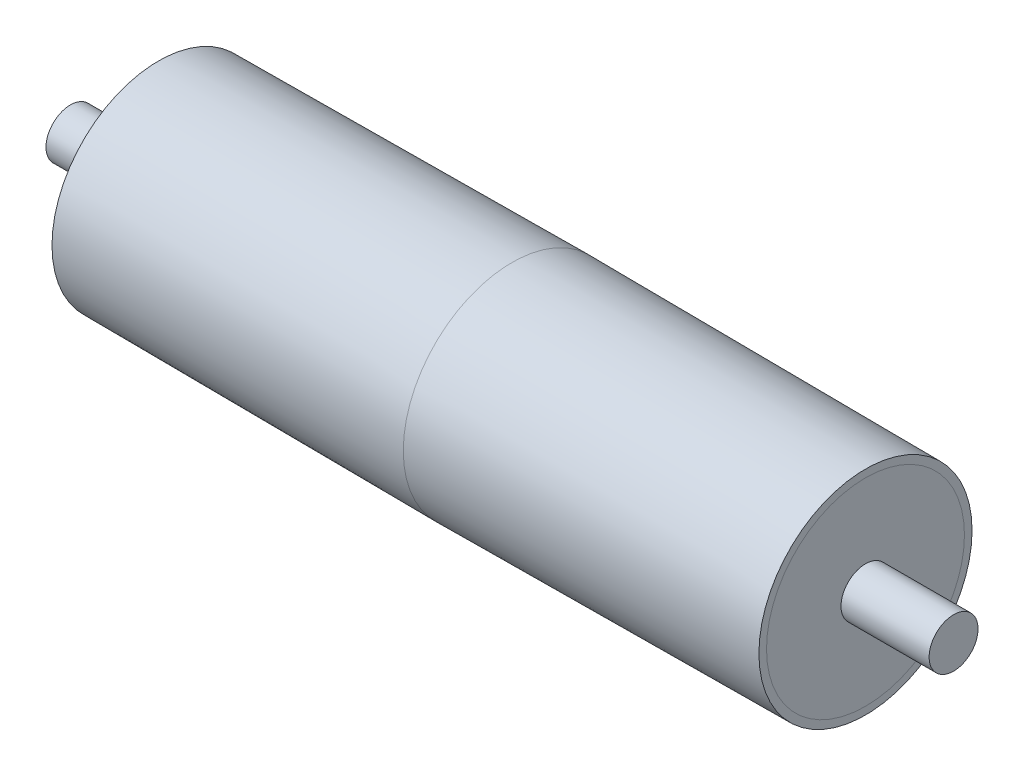
SolidWorks part; units mm, degrees
ref_plane "Front Plane" through (0, 0, 0) normal (0, 0, 1) x (1, 0, 0)
ref_plane "Top Plane" through (0, 0, 0) normal (0, 1, 0) x (1, 0, 0)
ref_plane "Right Plane" through (0, 0, 0) normal (1, 0, 0) x (0, 0, -1)
sketch "Sketch1" plane through (0, 0, 0) normal (0, 0, 1) x (1, 0, 0)
  line L0 (-325, 98) -> (325, 98) construction
  line L1 (-325, 98) -> (0, 100)
  line L2 (0, 0) -> (0, 98) construction
  line L3 (325, 98) -> (0, 100)
  line L4 (0, 0) -> (-22.4876, 0) construction
  line L5 (-325, 98) -> (-325, 0)
  line L6 (-325, 0) -> (325, 0)
  line L7 (325, 0) -> (325, 98)
  point P2 (0, 98)
  dimension "D1" = 2
  dimension "D2" = 650
  dimension "D3" = 100
revolve "Revolve1" add sketch "Sketch1" angle 360 about L6
shell "Shell1" thickness 7
sketch "Sketch2" plane through (325, 0, 0) normal (1, 0, 0) x (0, 0, -1)
  circle A0 centre (0, 0) radius 90.9999
  circle A1 centre (0, 0) radius 90.9999 construction
extrude "Boss-Extrude1" add sketch "Sketch2" against normal blind 10 separate body
mirror "Mirror2" about plane through (0, 0, 0) normal (1, 0, 0) of bodies 102
sketch "Sketch3" plane through (325, 0, 0) normal (1, 0, 0) x (0, 0, -1)
  circle A0 centre (0, 0) radius 22.5
  dimension "D1" = 45
extrude "Cut-Extrude1" cut sketch "Sketch3" against normal blind 735
sketch "Sketch4" plane through (0, 0, 0) normal (1, 0, 0) x (0, 0, -1)
  circle A0 centre (0, 0) radius 22.5
  circle A1 centre (0, 0) radius 22.5 construction
extrude "Boss-Extrude2" add sketch "Sketch4" along normal mid plane 812 separate body
